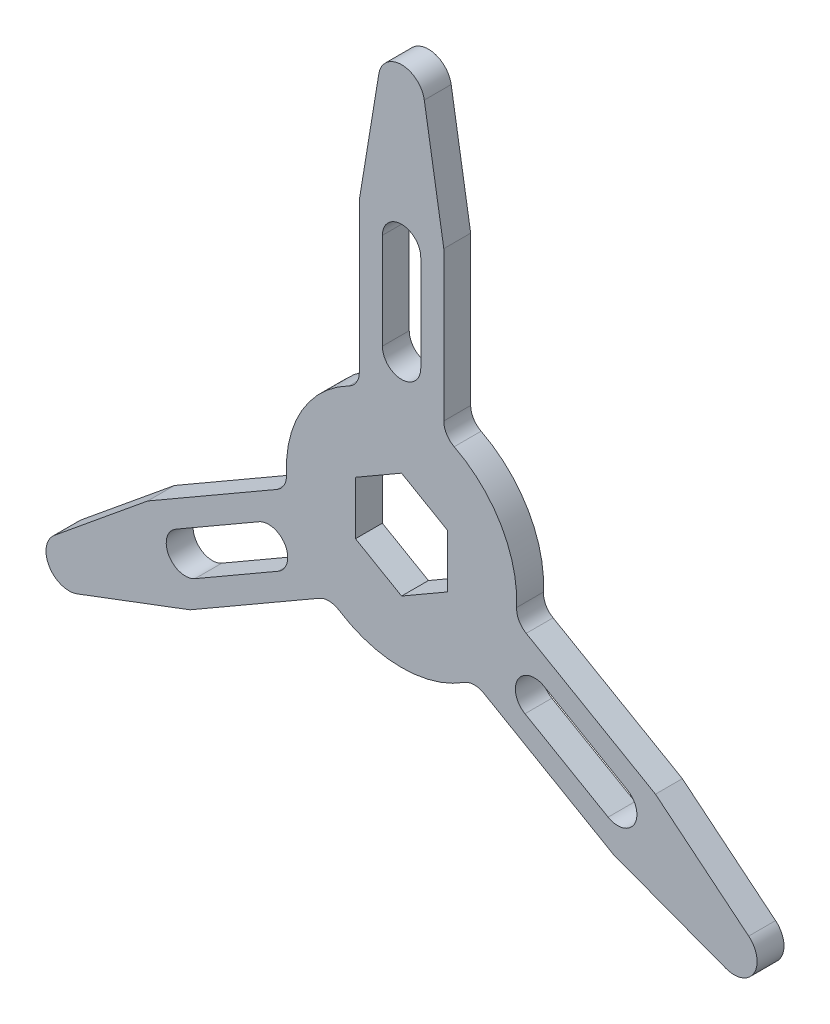
SolidWorks part; units mm, degrees
ref_plane "Přední rovina" through (0, 0, 0) normal (0, 0, 1) x (1, 0, 0)
ref_plane "Horní rovina" through (0, 0, 0) normal (0, 1, 0) x (1, 0, 0)
ref_plane "Pravá rovina" through (0, 0, 0) normal (1, 0, 0) x (0, 0, -1)
sketch "Skica1" plane through (0, 0, 0) normal (0, 0, 1) x (1, 0, 0)
  line L0 (0, 0) -> (0, 100) construction
  line L1 (0, 0) -> (-61.4144, -35.4576) construction
  line L2 (0, 0) -> (72.5786, -41.9033) construction
  line L3 (-5, 65) -> (-5, 40)
  line L4 (5, 65) -> (5, 40)
  line L5 (-11, 31.1288) -> (-11, 70)
  line L6 (11, 70) -> (11, 31.1288)
  line L7 (-11, 70) -> (-5.9209, 100.971)
  line L8 (11, 70) -> (5.9209, 100.971)
  line L9 (-12.3171, 100) -> (9.161, 100) construction
  line L10 (58.7917, -28.1699) -> (37.141, -15.6699)
  line L11 (0, -13.8564) -> (12, -6.9282)
  line L12 (12, -6.9282) -> (12, 6.9282)
  line L13 (12, 6.9282) -> (0, 13.8564)
  line L14 (0, 13.8564) -> (-12, 6.9282)
  line L15 (-12, 6.9282) -> (-12, -6.9282)
  line L16 (-12, -6.9282) -> (0, -13.8564)
  line L17 (53.7917, -36.8301) -> (32.141, -24.3301)
  line L18 (32.4583, -6.0381) -> (66.1218, -25.4737)
  line L19 (55.1218, -44.5263) -> (21.4583, -25.0907)
  line L20 (66.1218, -25.4737) -> (90.4039, -45.3578)
  line L21 (55.1218, -44.5263) -> (84.483, -55.6132)
  line L22 (92.7611, -39.3331) -> (82.0221, -57.9336) construction
  line L23 (-53.7917, -36.8301) -> (-32.141, -24.3301)
  line L24 (-58.7917, -28.1699) -> (-37.141, -15.6699)
  line L25 (-21.4583, -25.0907) -> (-55.1218, -44.5263)
  line L26 (-66.1218, -25.4737) -> (-32.4583, -6.0381)
  line L27 (-55.1218, -44.5263) -> (-84.483, -55.6132)
  line L28 (-66.1218, -25.4737) -> (-90.4039, -45.3578)
  line L29 (-80.444, -60.6669) -> (-91.183, -42.0664) construction
  arc A0 (-13.7143, 26.6818) -> (-29.9643, -1.464) centre (0, 0) ccw
  circle A1 centre (0, 0) radius 12 construction
  arc A2 (5.9209, 100.971) -> (-5.9209, 100.971) centre (0, 100) ccw
  arc A3 (5, 65) -> (-5, 65) centre (0, 65) ccw
  arc A4 (-5, 40) -> (5, 40) centre (0, 40) ccw
  arc A5 (11, 31.1288) -> (13.7143, 26.6818) centre (16, 31.1288) ccw
  arc A6 (-11, 31.1288) -> (-13.7143, 26.6818) centre (-16, 31.1288) cw
  arc A7 (84.483, -55.6132) -> (90.4039, -45.3578) centre (86.6025, -50) ccw
  arc A8 (53.7917, -36.8301) -> (58.7917, -28.1699) centre (56.2917, -32.5) ccw
  arc A9 (37.141, -15.6699) -> (32.141, -24.3301) centre (34.641, -20) ccw
  arc A10 (32.4583, -6.0381) -> (29.9643, -1.464) centre (34.9583, -1.708) cw
  arc A11 (21.4583, -25.0907) -> (16.25, -25.2178) centre (18.9583, -29.4208) ccw
  arc A12 (-90.4039, -45.3578) -> (-84.483, -55.6132) centre (-86.6025, -50) ccw
  arc A13 (-58.7917, -28.1699) -> (-53.7917, -36.8301) centre (-56.2917, -32.5) ccw
  arc A14 (-32.141, -24.3301) -> (-37.141, -15.6699) centre (-34.641, -20) ccw
  arc A15 (-21.4583, -25.0907) -> (-16.25, -25.2178) centre (-18.9583, -29.4208) cw
  arc A16 (-32.4583, -6.0381) -> (-29.9643, -1.464) centre (-34.9583, -1.708) ccw
  arc A17 (-16.25, -25.2178) -> (16.25, -25.2178) centre (0, 0) ccw
  arc A18 (29.9643, -1.464) -> (13.7143, 26.6818) centre (0, 0) ccw
  point P72 (0, 0)
  dimension "D1" = 60
  dimension "D2" = 24
  dimension "D5" = 6
  dimension "D7" = 25
  dimension "D12" = 5
  dimension "D3" = 120
  dimension "D4" = 120
  dimension "D6" = 10
  dimension "D8" = 40
  dimension "D9" = 22
  dimension "D10" = 70
  dimension "D11" = 30
  dimension "D13" = 3
extrude "Přidat vysunutím1" add sketch "Skica1" along normal blind 7
